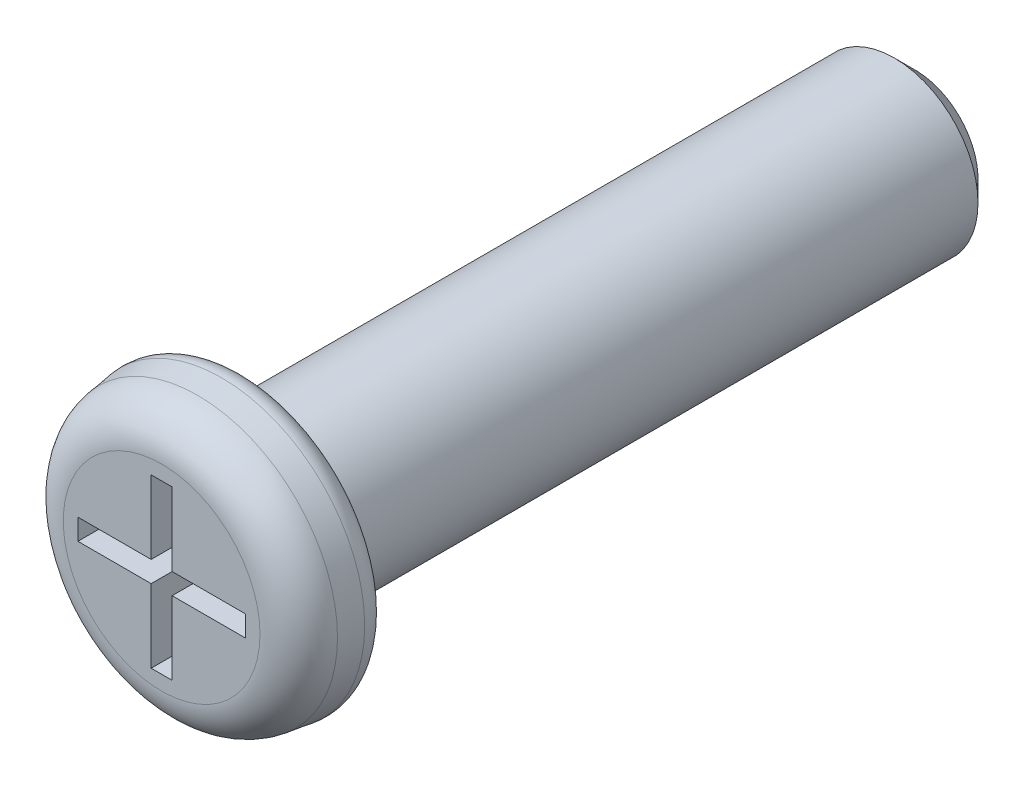
SolidWorks part; units mm, degrees
ref_plane "Plane1" through (0, 0, 0) normal (0, 0, 1) x (1, 0, 0)
ref_plane "Plane2" through (0, 0, 0) normal (0, 1, 0) x (1, 0, 0)
ref_plane "Plane3" through (0, 0, 0) normal (1, 0, 0) x (0, 0, -1)
sketch "Esquisse1" plane through (0, 0, 0) normal (0, 0, 1) x (1, 0, 0)
  circle A0 centre (0, 0) radius 1.75
  dimension "D1" = 3.5
extrude "Base-Extrusion" add sketch "Esquisse1" along normal blind 1 draft 8
fillet "Congé1" radius 0.5
sketch "Esquisse2" plane through (0, 0, 0) normal (0, 0, -1) x (-1, 0, 0)
  circle A0 centre (0, 0) radius 1
  dimension "D1" = 2
extrude "Boss.-Extru.1" add sketch "Esquisse2" along normal blind 8
chamfer "Chanfrein1" distance 0.25 angle 45
sketch "Esquisse3" plane through (0, 0, 1) normal (0, 0, 1) x (1, 0, 0)
  line L0 (0, 0) -> (0, 1) construction
  line L1 (-0.125, 1) -> (-0.125, 0.125)
  line L2 (0.125, 1) -> (0.125, 0.125)
  line L3 (0.125, 1) -> (-0.125, 1)
  line L4 (1, -0.125) -> (1, 0.125)
  line L5 (1, -0.125) -> (0.125, -0.125)
  line L6 (1, 0.125) -> (0.125, 0.125)
  line L7 (-0.125, -1) -> (0.125, -1)
  line L8 (-0.125, -1) -> (-0.125, -0.125)
  line L9 (0.125, -1) -> (0.125, -0.125)
  line L10 (-1, 0.125) -> (-1, -0.125)
  line L11 (-1, 0.125) -> (-0.125, 0.125)
  line L12 (-1, -0.125) -> (-0.125, -0.125)
extrude "Enlèv. mat.-Extru.1" cut sketch "Esquisse3" against normal blind 0.5
fillet "Congé2" radius 0.25
